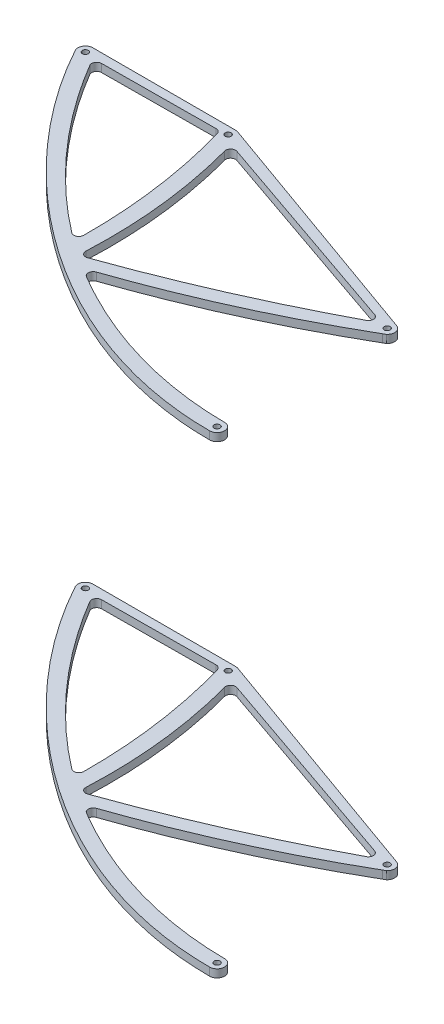
SolidWorks part; units mm, degrees
material "7075-O (SS)"
ref_plane "Płaszczyzna XY" through (0, 0, 0) normal (0, 0, 1) x (1, 0, 0)
ref_plane "Płaszczyzna XZ" through (0, 0, 0) normal (0, 1, 0) x (1, 0, 0)
ref_plane "Płaszczyzna YZ" through (0, 0, 0) normal (1, 0, 0) x (0, 0, -1)
ref_plane "Płaszczyzna1" through (0, -230, 0) normal (0, 1, 0) x (1, 0, 0)
sketch "Szkic1" plane through (0, -230, 0) normal (0, 1, 0) x (1, 0, 0)
  line L0 (-860.2838, -96.903) -> (-716.3676, -96.903)
  line L1 (-459.645, -364.8201) -> (-459.645, -193.4029)
  line L2 (-464.6227, -186.3398) -> (-713.8453, -97.3399)
  arc A0 (-860.2838, -96.903) -> (-866.571, -108.4922) centre (-860.2838, -104.403) ccw
  circle A1 centre (-860.2838, -104.403) radius 3
  arc A2 (-713.8453, -97.3399) -> (-716.3676, -96.903) centre (-716.3676, -104.403) ccw
  circle A3 centre (-716.3676, -104.403) radius 3
  arc A4 (-467.145, -372.3201) -> (-459.645, -364.8201) centre (-467.145, -364.8201) ccw
  circle A5 centre (-467.145, -364.8201) radius 3
  arc A6 (-459.645, -193.4029) -> (-464.6227, -186.3398) centre (-467.145, -193.4029) ccw
  circle A7 centre (-467.145, -193.4029) radius 3
  spline S0 degree 3 poles (-866.571, -108.4922) (-792.0064, -245.3785) (-630.8215, -372.3201) (-467.145, -372.3201) knots 0 0 0 0 1 1 1 1
  dimension "D1" = 15
  dimension "D2" = 6
  dimension "D5" = 6
  dimension "D6" = 15
  dimension "D3" = 15
  dimension "D4" = 6
  dimension "D7" = 15
  dimension "D8" = 6
extrude "Dodanie-wyciągnięcie1" add sketch "Szkic1" against normal blind 8
sketch "Szkic2" plane through (0, 0, 0) normal (1, 0, 0) x (0, 0, -1)
  line L0 (-104.403, -238) -> (-104.403, -230)
  line L1 (-186.3398, -238) -> (-97.3399, -238) construction
  line L2 (151.4794, -230) -> (-151.4794, -230) construction
  dimension "D1" = 7.5
split line "Linia podziałowa1"
sketch "Szkic3" plane through (0, -230, 0) normal (0, 1, 0) x (1, 0, 0)
  line L0 (-727.5928, -105.3408) -> (-842.2139, -106.165)
  line L1 (-464.6227, -186.3398) -> (-713.8453, -97.3399) construction
  line L2 (-716.3676, -96.903) -> (-860.2838, -96.903) construction
  line L3 (-464.6227, -186.3398) -> (-713.8453, -97.3399)
  line L4 (-716.3676, -96.903) -> (-860.2838, -96.903)
  line L5 (-697.3361, -114.6625) -> (-485.2524, -187.8322)
  line L6 (-464.6227, -200.466) -> (-462.2867, -199.1166)
  line L7 (-459.645, -364.8201) -> (-459.645, -193.4029) construction
  line L8 (-459.645, -364.8201) -> (-459.645, -193.4029)
  circle A0 centre (-860.2838, -104.403) radius 2.5
  circle A1 centre (-716.3676, -104.403) radius 2.5
  circle A2 centre (-467.145, -193.4029) radius 2.5
  circle A3 centre (-467.145, -364.8201) radius 2.5
  arc A4 (-860.2838, -96.903) -> (-866.571, -108.4922) centre (-860.2838, -104.403) ccw
  arc A5 (-713.8453, -97.3399) -> (-716.3676, -96.903) centre (-716.3676, -104.403) ccw
  arc A6 (-462.2867, -199.1166) -> (-464.6227, -186.3398) centre (-467.145, -193.4029) ccw
  arc A7 (-467.145, -372.3201) -> (-465.5643, -357.4886) centre (-467.145, -364.8201) ccw
  arc A8 (-727.5928, -105.3408) -> (-722.7513, -108.9599) centre (-727.5568, -110.3407) cw
  arc A9 (-709.2485, -269.0767) -> (-701.2158, -265.1334) centre (-706.2157, -265.1015) ccw
  arc A10 (-842.2139, -106.165) -> (-846.4803, -113.7124) centre (-842.178, -111.1649) ccw
  arc A11 (-484.5448, -196.9784) -> (-485.2524, -187.8322) centre (-486.8831, -192.5588) ccw
  arc A12 (-697.3361, -114.6625) -> (-703.7908, -120.704) centre (-698.9668, -119.3892) ccw
  arc A13 (-679.6467, -282.7954) -> (-686.3192, -277.8605) centre (-681.3242, -278.0852) cw
  arc A14 (-662.8286, -290.8502) -> (-663.7572, -299.874) centre (-661.1998, -295.5775) ccw
  spline S0 degree 3 poles (1018.2834, -430.2749) (-2895.0892, 1790.6073) (443.0725, -2697.7026) (-45.9349, 1511.8105) knots -2.300472 -2.300472 -2.300472 -2.300472 2.787148 2.787148 2.787148 2.787148 only from (-866.571, -108.4922) to (-467.145, -372.3201) construction
  spline S1 degree 3 poles (-866.571, -108.4922) (-792.0064, -245.3785) (-630.8215, -372.3201) (-467.145, -372.3201) knots 0 0 0 0 1 1 1 1
  spline S2 degree 3 poles (-465.5643, -357.4886) (-536.6766, -357.1012) (-603.9737, -335.4588) (-663.7572, -299.874) knots 0 0 0 0 0.430291 0.430291 0.430291 0.430291
  spline S3 degree 3 poles (-464.6227, -200.466) (-496.5561, -218.9126) (-561.1985, -252.192) (-628.7244, -279.1) (-662.8286, -290.8502) knots 0 0 0 0 0.48193 0.953575 0.953575 0.953575 0.953575
  spline S4 degree 3 poles (-679.6467, -282.7954) (-646.393, -270.9519) (-580.3187, -244.7221) (-516.3066, -213.7825) (-484.5448, -196.9784) knots 0.032175 0.032175 0.032175 0.032175 0.487326 0.950668 0.950668 0.950668 0.950668
  spline S5 degree 3 poles (-686.3192, -277.8605) (-685.3029, -255.2694) (-686.3947, -202.3872) (-695.7057, -150.3677) (-703.7908, -120.704) knots 0.039857 0.039857 0.039857 0.039857 0.403728 0.897513 0.897513 0.897513 0.897513
  spline S6 degree 3 poles (-701.2158, -265.1334) (-701.0774, -243.4237) (-703.8201, -190.8252) (-714.0788, -139.1428) (-722.7513, -108.9599) knots 0.056949 0.056949 0.056949 0.056949 0.434452 0.978099 0.978099 0.978099 0.978099
  spline S7 degree 3 poles (-709.2485, -269.0767) (-722.1797, -259.2108) (-775.604, -214.1624) (-819.7462, -158.864) (-846.4803, -113.7124) knots 0.543325 0.543325 0.543325 0.543325 0.643435 0.972152 0.972152 0.972152 0.972152
  dimension "D1" = 5
  dimension "D2" = 5
  dimension "D3" = 5
  dimension "D4" = 5
  dimension "D5" = 5
  dimension "D6" = 5
  dimension "D7" = 5
extrude "Wytnij-wyciągnięcie1" cut sketch "Szkic3" against normal blind 10 contours S7 A9 S6 A8 L0 A10 | S5 A13 S4 A11 L5 A12 | L6 S3 A14 S2 A7 L8 A6
mirror "Lustro1" about plane through (0, 0, 0) normal (0, 1, 0) of bodies 104
